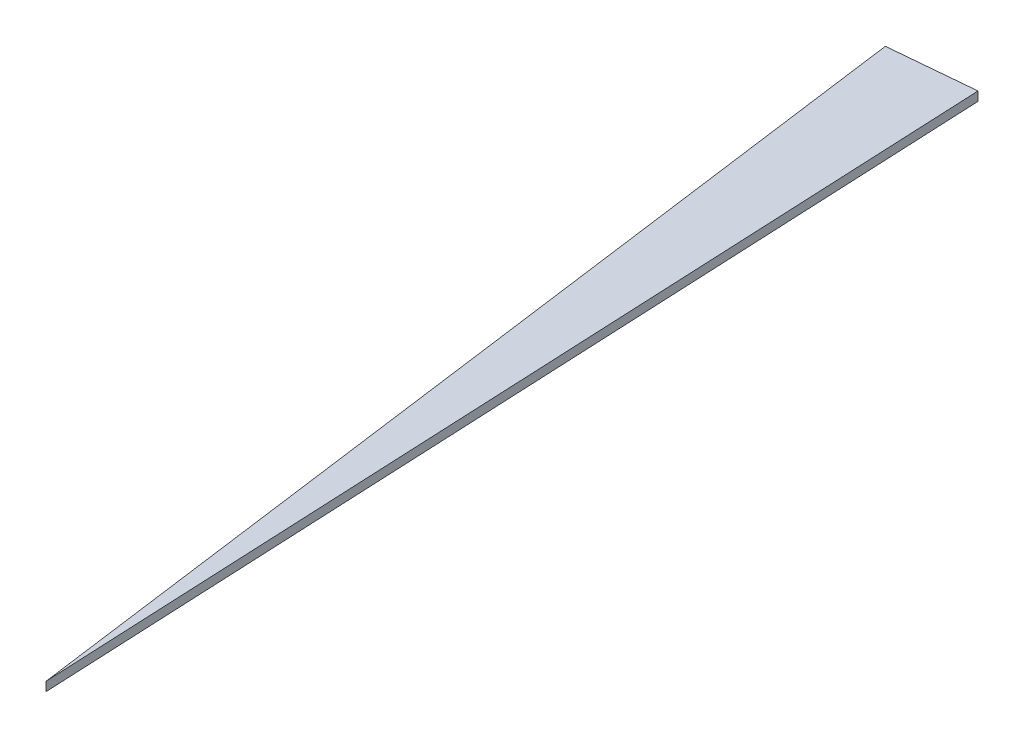
SolidWorks part; units mm, degrees
ref_plane "Front Plane" through (0, 0, 0) normal (0, 0, 1) x (1, 0, 0)
ref_plane "Top Plane" through (0, 0, 0) normal (0, 1, 0) x (1, 0, 0)
ref_plane "Right Plane" through (0, 0, 0) normal (1, 0, 0) x (0, 0, -1)
sketch "Sketch1" plane through (0, 0, 0) normal (0, 1, 0) x (1, 0, 0)
  line L0 (0, 0) -> (-8.6536, 64.4214)
  line L1 (0, 0) -> (-3.006, 64.9305)
  line L2 (-8.6536, 64.4214) -> (-3.006, 64.9305)
  dimension "D1" = 65
  dimension "D2" = 65
  dimension "D3" = 5
extrude "Boss-Extrude1" add sketch "Sketch1" along normal blind 0.6
ref_plane "Plane1" through (0, 0.3, 0) normal (0, 1, 0) x (1, 0, 0)
